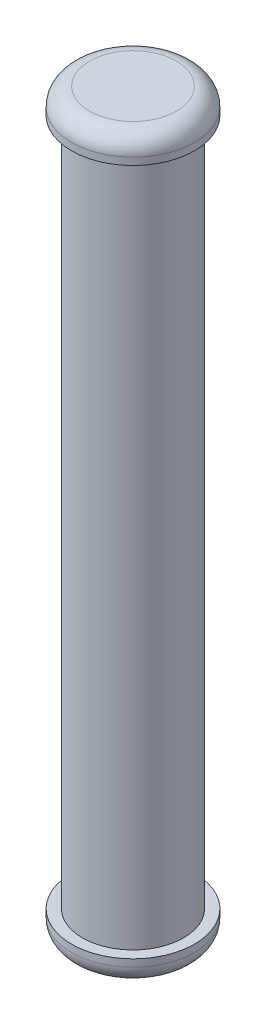
SolidWorks part; units mm, degrees
ref_plane "Front Plane" through (0, 0, 0) normal (0, 0, 1) x (1, 0, 0)
ref_plane "Top Plane" through (0, 0, 0) normal (0, 1, 0) x (1, 0, 0)
ref_plane "Right Plane" through (0, 0, 0) normal (1, 0, 0) x (0, 0, -1)
sketch "Sketch1" plane through (0, 0, 0) normal (0, 1, 0) x (1, 0, 0)
  circle A0 centre (0, 0) radius 1.4
  dimension "D1" = 2.8
extrude "Boss-Extrude1" add sketch "Sketch1" along normal blind 19
sketch "Sketch2" plane through (0, 19, 0) normal (0, 1, 0) x (1, 0, 0)
  circle A0 centre (0, 0) radius 1.7
  dimension "D1" = 3.4
extrude "Boss-Extrude2" add sketch "Sketch2" along normal blind 0.7
fillet "Fillet1" radius 0.5 1 edges at (0, 19.7, 1.7)
sketch "Sketch3" plane through (0, 0, 0) normal (0, -1, 0) x (1, 0, 0)
  circle A0 centre (0, 0) radius 1.7
  dimension "D1" = 3.4
extrude "Boss-Extrude3" add sketch "Sketch3" along normal blind 0.7
fillet "Fillet2" radius 0.5 1 edges at (0, -0.7, -1.7)
